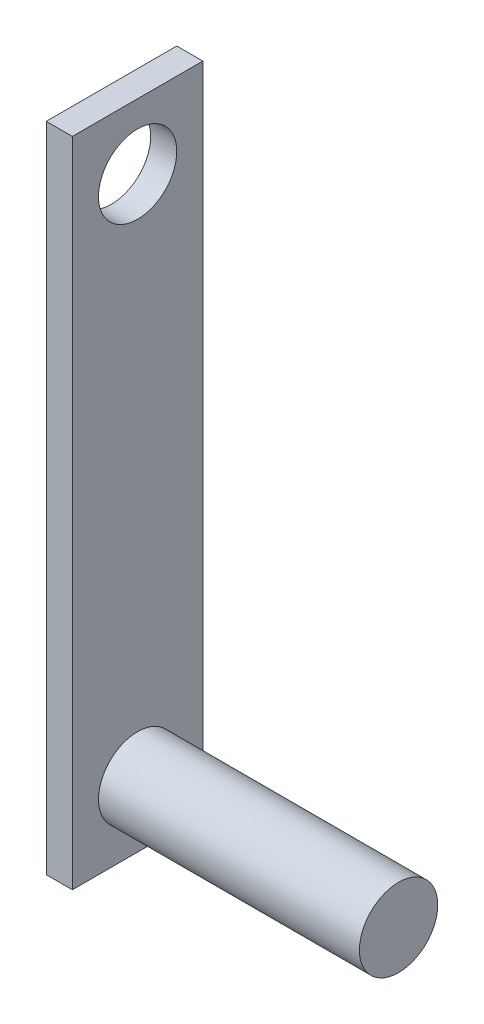
SolidWorks part; units mm, degrees
ref_plane "Front Plane" through (0, 0, 0) normal (0, 0, 1) x (1, 0, 0)
ref_plane "Top Plane" through (0, 0, 0) normal (0, 1, 0) x (1, 0, 0)
ref_plane "Right Plane" through (0, 0, 0) normal (1, 0, 0) x (0, 0, -1)
sketch "Sketch1" plane through (0, 0, 0) normal (1, 0, 0) x (0, 0, -1)
  line L1 (-5, -25) -> (5, -25)
  line L2 (-5, -25) -> (-5, 25)
  line L3 (-5, 25) -> (5, 25)
  line L4 (5, -25) -> (5, 25)
  line L5 (-5, -25) -> (5, 25) construction
  line L6 (-5, 25) -> (5, -25) construction
  point P0 (0, 0)
  dimension "D1" = 50
  dimension "D2" = 10
extrude "Boss-Extrude1" add sketch "Sketch1" along normal blind 2
sketch "Sketch2" plane through (2, 0, 0) normal (1, 0, 0) x (0, 0, -1)
  circle A0 centre (0, 20) radius 3
extrude "Cut-Extrude1" cut sketch "Sketch2" against normal up to surface (2 mm away) up to face at (0, 0, 0)
sketch "Sketch3" plane through (2, 0, 0) normal (1, 0, 0) x (0, 0, -1)
  circle A0 centre (0, -20) radius 3
extrude "Boss-Extrude2" add sketch "Sketch3" along normal blind 20
